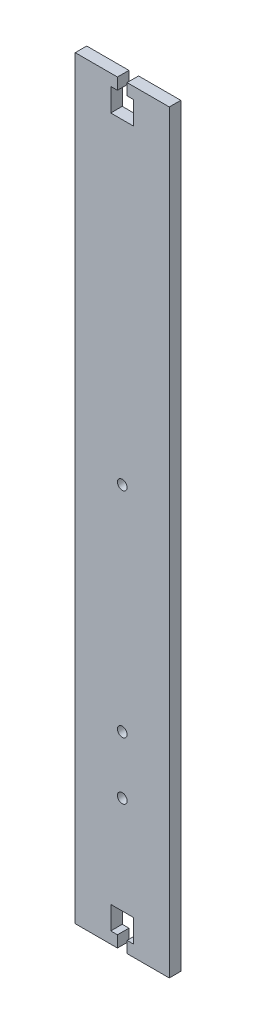
SolidWorks part; units mm, degrees
ref_plane "Front Plane" through (0, 0, 0) normal (0, 0, 1) x (1, 0, 0)
ref_plane "Top Plane" through (0, 0, 0) normal (0, 1, 0) x (1, 0, 0)
ref_plane "Right Plane" through (0, 0, 0) normal (1, 0, 0) x (0, 0, -1)
sketch "Sketch1" plane through (0, 0, 0) normal (0, 0, 1) x (1, 0, 0)
  line L1 (20.445, -164) -> (-20.445, -164)
  line L2 (20.445, -164) -> (20.445, 164)
  line L3 (20.445, 164) -> (-20.445, 164)
  line L4 (-20.445, -164) -> (-20.445, 164)
  line L5 (20.445, -164) -> (-20.445, 164) construction
  line L6 (20.445, 164) -> (-20.445, -164) construction
  point P0 (0, 0)
  dimension "D1" = 328
  dimension "D2" = 40.89
extrude "Boss-Extrude1" add sketch "Sketch1" along normal blind 5
sketch "Sketch2" plane through (0, 0, 5) normal (0, 0, 1) x (1, 0, 0)
  line L2 (20.445, -164) -> (20.445, 164) construction
  line L3 (20.445, -81.5) -> (-20.445, -81.5) construction
  line L4 (-20.445, 164) -> (-20.445, -164) construction
  circle A0 centre (0, -81.5) radius 2.1
  dimension "D1" = 4.2
extrude "Cut-Extrude1" cut sketch "Sketch2" against normal blind 10
sketch "Sketch3" plane through (0, 0, 5) normal (0, 0, 1) x (1, 0, 0)
  line L0 (0, -164) -> (0, -133.9684) construction
  line L1 (-20.445, -164) -> (20.445, -164) construction
  line L2 (20.445, 0) -> (-17.01, 0) construction
  line L3 (20.445, -164) -> (20.445, 164) construction
  line L4 (-2.1, -164) -> (-2.1, -159)
  line L5 (-2.1, -159) -> (-5, -159)
  line L6 (-5, -159) -> (-5, -149)
  line L7 (-5, -149) -> (5, -149)
  line L8 (-2.1, -164) -> (2.1, -164)
  line L9 (5, -159) -> (5, -149)
  line L10 (2.1, -159) -> (5, -159)
  line L11 (2.1, -164) -> (2.1, -159)
  line L12 (0, 164) -> (0, 133.9684) construction
  line L13 (2.1, 164) -> (2.1, 159)
  line L14 (2.1, 159) -> (5, 159)
  line L15 (5, 159) -> (5, 149)
  line L16 (-2.1, 164) -> (2.1, 164)
  line L17 (-5, 149) -> (5, 149)
  line L18 (-5, 159) -> (-5, 149)
  line L19 (-2.1, 159) -> (-5, 159)
  line L20 (-2.1, 164) -> (-2.1, 159)
  point P16 (0, -149)
  point P28 (0, 149)
  dimension "D1" = 10
  dimension "D2" = 5
  dimension "D3" = 5
  dimension "D4" = 4.2
extrude "Cut-Extrude2" cut sketch "Sketch3" against normal blind 10
sketch "Sketch4" plane through (0, 0, 5) normal (0, 0, 1) x (1, 0, 0)
  line L2 (-20.445, 164) -> (-20.445, -164) construction
  line L3 (-20.445, -106.5) -> (20.445, -106.5) construction
  line L4 (20.445, -164) -> (20.445, 164) construction
  circle A0 centre (0, -106.5) radius 2.1
  dimension "D1" = 4.2
extrude "Cut-Extrude3" cut sketch "Sketch4" against normal blind 5
sketch "Sketch5" plane through (0, 0, 5) normal (0, 0, 1) x (1, 0, 0)
  line L2 (-20.445, 164) -> (-20.445, -164) construction
  line L3 (-20.445, 11.5) -> (20.445, 11.5) construction
  line L4 (20.445, -164) -> (20.445, 164) construction
  circle A0 centre (0, 11.5) radius 2.1
  dimension "D1" = 4.2
extrude "Cut-Extrude4" cut sketch "Sketch5" against normal blind 5
